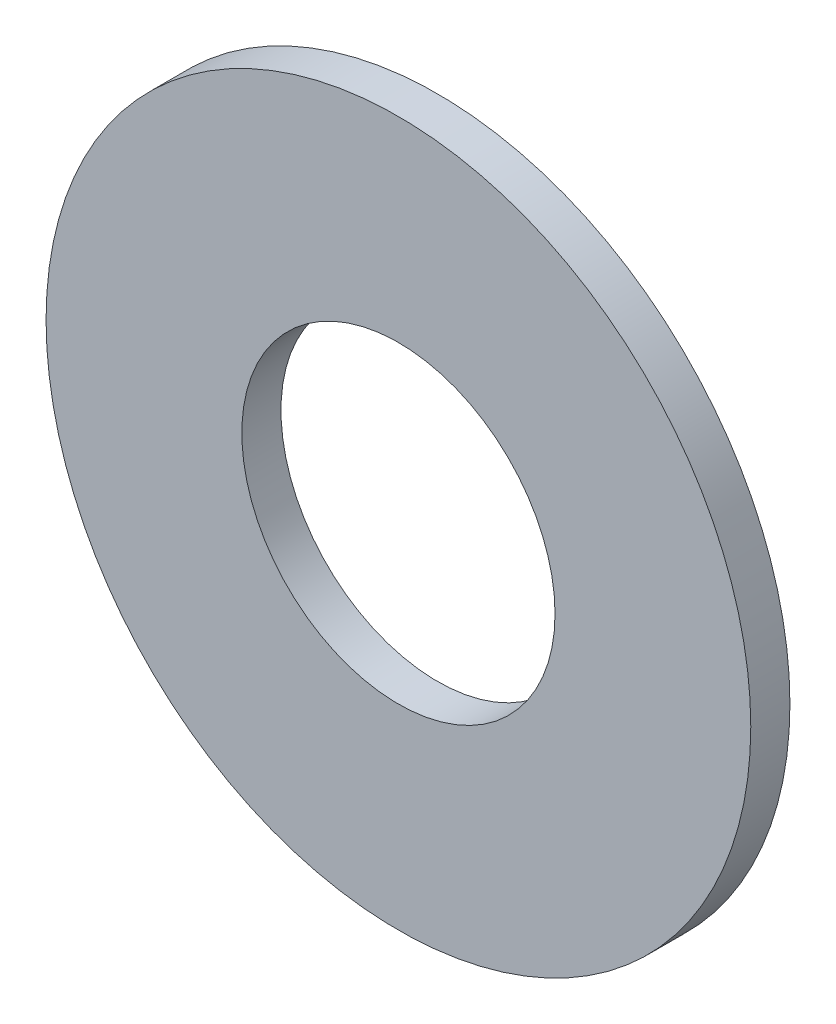
SolidWorks part; units mm, degrees
material "6061 合金"
ref_plane "前视基准面" through (0, 0, 0) normal (0, 0, 1) x (1, 0, 0)
ref_plane "上视基准面" through (0, 0, 0) normal (0, 1, 0) x (1, 0, 0)
ref_plane "右视基准面" through (0, 0, 0) normal (1, 0, 0) x (0, 0, -1)
sketch "草图1" plane through (0, 0, 0) normal (0, 0, 1) x (1, 0, 0)
  circle A0 centre (0, 0) radius 4.5
  circle A1 centre (0, 0) radius 2
  dimension "D1" = 9
  dimension "D2" = 4
extrude "凸台-拉伸1" add sketch "草图1" along normal blind 0.5
